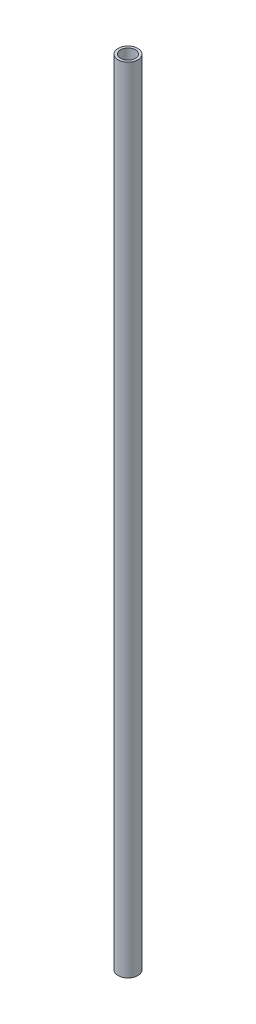
SolidWorks part; units mm, degrees
ref_plane "Front Plane" through (0, 0, 0) normal (0, 0, 1) x (1, 0, 0)
ref_plane "Top Plane" through (0, 0, 0) normal (0, 1, 0) x (1, 0, 0)
ref_plane "Right Plane" through (0, 0, 0) normal (1, 0, 0) x (0, 0, -1)
sketch "Sketch1" plane through (0, 0, 0) normal (0, 1, 0) x (1, 0, 0)
  circle A0 centre (0, 0) radius 1.5
  circle A1 centre (0, 0) radius 2
  dimension "D1" = 3
  dimension "D2" = 4
extrude "Boss-Extrude1" add sketch "Sketch1" along normal blind 160
